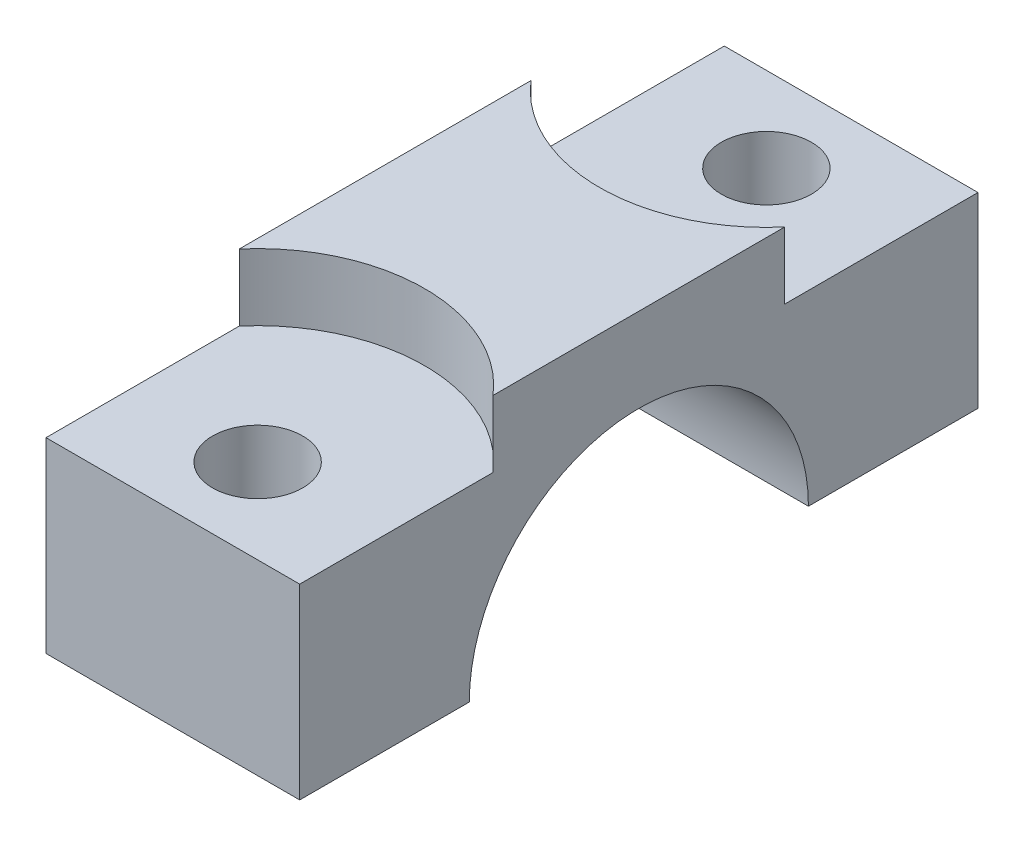
SolidWorks part; units mm, degrees
ref_plane "Alzado" through (0, 0, 0) normal (0, 0, 1) x (1, 0, 0)
ref_plane "Planta" through (0, 0, 0) normal (0, 1, 0) x (1, 0, 0)
ref_plane "Vista lateral" through (0, 0, 0) normal (1, 0, 0) x (0, 0, -1)
sketch "Croquis1" plane through (0, 0, 0) normal (1, 0, 0) x (0, 0, -1)
  line L1 (-25.4, 0) -> (25.4, 0)
  line L2 (-25.4, 0) -> (-25.4, 19)
  line L3 (-25.4, 19) -> (25.4, 19)
  line L4 (25.4, 0) -> (25.4, 19)
  circle A0 centre (0, 0) radius 12.7
  dimension "D1" = 50.8
  dimension "D3" = 25.4
  dimension "D2" = 19
extrude "Saliente-Extruir1" add sketch "Croquis1" along normal mid plane 19 contours A0 L1 L4 L3 L2
sketch "Croquis2" plane through (0, 0, 0) normal (0, -1, 0) x (1, 0, 0)
  line L0 (0, 25.4) -> (0, 12.7) construction
  line L1 (9.5, 25.4) -> (-9.5, 25.4) construction
  line L2 (9.5, 12.7) -> (-9.5, 12.7) construction
  line L3 (0, -12.7) -> (0, -25.4) construction
  line L4 (9.5, -12.7) -> (-9.5, -12.7) construction
  line L5 (9.5, -25.4) -> (-9.5, -25.4) construction
  point P12 (0, 19.05)
  point P13 (0, -19.05)
hole_wizard "Refrentado para tornillo con cabeza hueca hexagonal de M121" positions "Croquis5" profile "Croquis4" counterbore size "M12" standard "ISO" end condition through all
sketch "Croquis5" plane through (0, 19, 0) normal (0, 1, 0) x (1, 0, 0)
  line L0 (0, 12.7) -> (0, 25.4) construction
  point P0 (0, -19.05)
  point P3 (0, 19.05)
sketch "Croquis4" plane through (0, 19, 19.05) normal (1, 0, 0) x (0, 0, 1)
  line L0 (0, 0) -> (0, 19)
  line L1 (0, 19) -> (3.375, 19)
  line L3 (3.375, 19) -> (3.375, 5)
  line L4 (3.375, 5) -> (12.5, 5)
  line L5 (12.5, 5) -> (12.5, 0)
  line L7 (12.5, 0) -> (0, 0)
  line L11 (0, -6.35) -> (0, 107.95) construction
  dimension "Diámetro de taladro hasta el siguiente" = 6.75
  dimension "Profundidad de taladro hasta el siguiente" = 19
  dimension "Diámetro de refrentado" = 25
  dimension "Profundidad de refrentado" = 5
